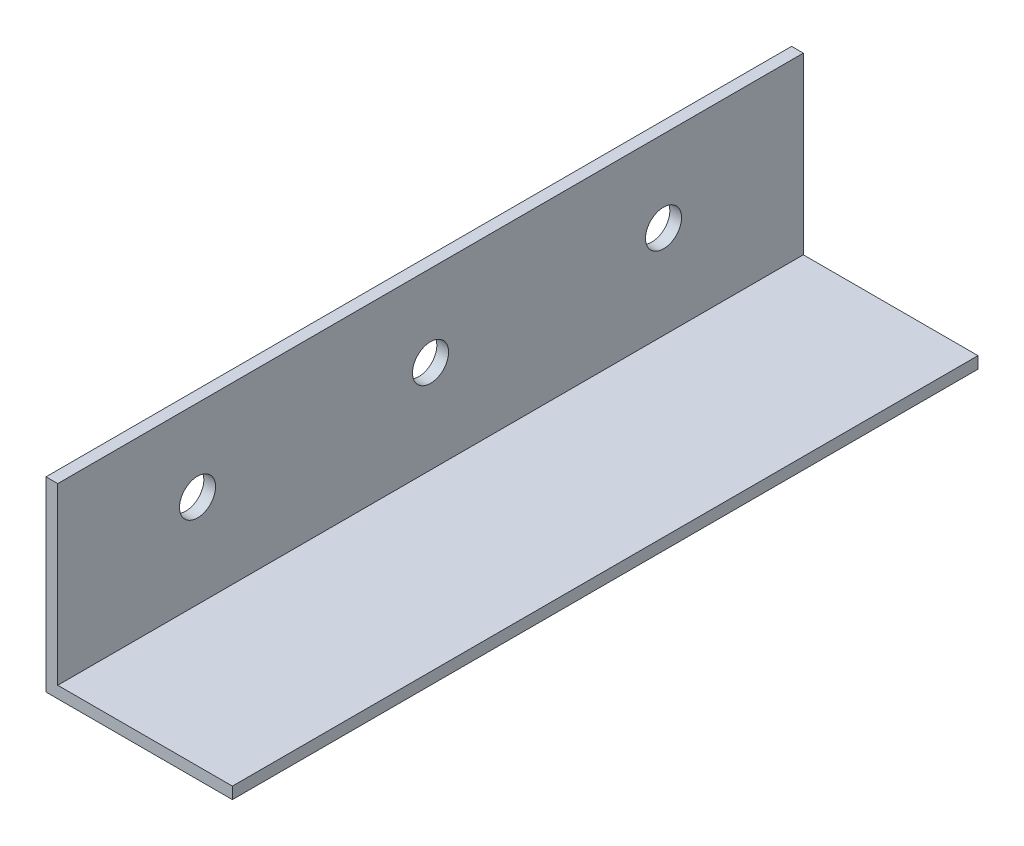
SolidWorks part; units mm, degrees
material "6061-T6 (SS)"
ref_plane "Front Plane" through (0, 0, 0) normal (0, 0, 1) x (1, 0, 0)
ref_plane "Top Plane" through (0, 0, 0) normal (0, 1, 0) x (1, 0, 0)
ref_plane "Right Plane" through (0, 0, 0) normal (1, 0, 0) x (0, 0, -1)
sketch "Sketch1" plane through (0, 0, 0) normal (0, 0, 1) x (1, 0, 0)
  line L0 (0, 0) -> (0, 25.4)
  line L1 (0, 25.4) -> (1.6002, 25.4)
  line L2 (1.6002, 25.4) -> (1.6002, 1.6002)
  line L3 (1.6002, 1.6002) -> (25.4, 1.6002)
  line L4 (25.4, 1.6002) -> (25.4, 0)
  line L5 (25.4, 0) -> (0, 0)
  dimension "D1" = 1.6002
  dimension "D2" = 25.4
extrude "Boss-Extrude1" add sketch "Sketch1" along normal blind 101.6 contours L2 L3 L4 L5 L0 L1
hole_wizard "#10 (0.1935) Diameter Hole1" positions "Sketch3" profile "Sketch2" hole size "#10" standard "ANSI Inch" end condition through all
sketch "Sketch3" plane through (1.6002, 0, 0) normal (1, 0, 0) x (0, 0, -1)
  line L0 (-101.6, 25.4) -> (-101.6, 1.6002) construction
  line L1 (0, 25.4) -> (0, 1.6002) construction
  line L5 (-101.6, 0) -> (0, 0) construction
  point P0 (-82.55, 14.2875)
  point P2 (-50.8, 14.2875)
  point P4 (-19.05, 14.2875)
  point P9 (0, 13.5001)
  point P16 (0, 13.5001)
  dimension "D1" = 19.05
  dimension "D2" = 19.05
  dimension "D3" = 50.8
  dimension "D4" = 14.2875
sketch "Sketch2" plane through (1.6002, 14.2875, 82.55) normal (0, 1, 0) x (0, 0, -1)
  line L0 (0, 0) -> (0, 1.6002)
  line L1 (0, 1.6002) -> (2.4574, 1.6002)
  line L2 (2.4574, 1.6002) -> (2.4574, 0)
  line L5 (2.4574, 0) -> (0, 0)
  line L11 (0, -6.35) -> (0, 107.95) construction
  dimension "Thru Hole Dia." = 4.9149
  dimension "Thru Hole Depth" = 1.6002
